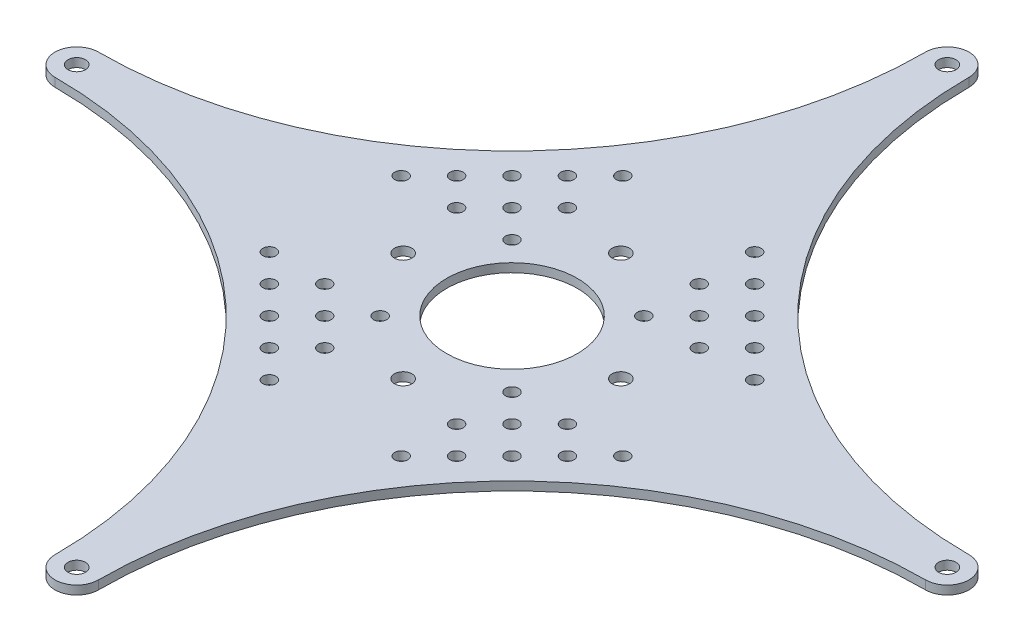
SolidWorks part; units mm, degrees
ref_plane "Front" through (0, 0, 0) normal (0, 0, 1) x (1, 0, 0)
ref_plane "Top" through (0, 0, 0) normal (0, 1, 0) x (1, 0, 0)
ref_plane "Right" through (0, 0, 0) normal (1, 0, 0) x (0, 0, -1)
sketch "Эскиз1" plane through (0, 0, 0) normal (0, 1, 0) x (1, 0, 0)
  line L0 (-100, 0) -> (0, 0) construction
  line L1 (0, 0) -> (100, 0) construction
  line L2 (100, 0) -> (0, 0) construction
  line L3 (0, 100) -> (0, 0) construction
  line L4 (0, -100) -> (0, 0) construction
  arc A0 (-5, 100) -> (5, 100) centre (0, 100) cw
  arc A1 (-100, -5) -> (-100, 5) centre (-100, 0) cw
  arc A2 (-100, 5) -> (-5, 100) centre (-100, 100) ccw
  arc A3 (-5, -100) -> (5, -100) centre (0, -100) ccw
  arc A4 (100, 5) -> (100, -5) centre (100, 0) cw
  arc A5 (-100, -5) -> (-5, -100) centre (-100, -100) cw
  arc A6 (100, -5) -> (5, -100) centre (100, -100) ccw
  arc A7 (5, 100) -> (100, 5) centre (100, 100) ccw
  dimension "D1" = 5
  dimension "D2" = 95
  dimension "D3" = 200
extrude "основа" add sketch "Эскиз1" along normal blind 2
sketch "Эскиз2" plane through (0, 2, 0) normal (0, 1, 0) x (1, 0, 0)
  line L0 (100, 0) -> (0, 0) construction
  circle A0 centre (100, 0) radius 2
  arc A4 (100, -5) -> (100, 5) centre (100, 0) ccw construction
  circle A5 centre (25, 0) radius 2
  dimension "D1" = 4
  dimension "D2" = 75
extrude "отверстия под балку" cut sketch "Эскиз2" against normal through all
sketch "ось" plane through (0, 0, 0) normal (1, 0, 0) x (0, 0, -1)
  line L0 (0, 2) -> (0, 0) construction
  line L1 (5, 2) -> (-5, 2) construction
pattern_circular "отверстия под балки" count 4 over 360 about axis through (0, 0, 0) along (0, 1, 0) of "отверстия под балку"
sketch "Эскиз4" plane through (0, 2, 0) normal (0, 1, 0) x (1, 0, 0)
  circle A0 centre (0, 0) radius 15
  dimension "D1" = 30
extrude "отверстие центр" cut sketch "Эскиз4" against normal through all
sketch "Эскиз5" plane through (0, 2, 0) normal (0, 1, 0) x (1, 0, 0)
  line L0 (0, 0) -> (32.8249, 32.8249) construction
  line L1 (40.603, 15.1472) -> (27.8751, 27.8751) construction
  circle A0 centre (40.603, 15.1472) radius 1.5
  circle A1 centre (34.2391, 8.7832) radius 1.5 [skipped]
  circle A2 centre (27.8751, 2.4193) radius 1.5 [skipped]
  circle A3 centre (27.8751, 15.1472) radius 1.5
  arc A4 (5, 100) -> (100, 5) centre (100, 100) ccw construction
  circle A6 centre (21.5111, 8.7832) radius 1.5 [skipped]
  circle A7 centre (21.5111, 21.5111) radius 1.5
  circle A8 centre (15.1472, 15.1472) radius 1.5
  circle A9 centre (15.1472, 27.8751) radius 1.5
  circle A10 centre (8.7832, 21.5111) radius 1.5 [skipped]
  circle A11 centre (8.7832, 34.2391) radius 1.5 [skipped]
  circle A12 centre (2.4193, 27.8751) radius 1.5 [skipped]
  circle A13 centre (34.2391, 21.5111) radius 1.5
  circle A14 centre (27.8751, 27.8751) radius 1.5
  circle A15 centre (21.5111, 34.2391) radius 1.5
  circle A16 centre (15.1472, 40.603) radius 1.5
  dimension "D1" = 18
  dimension "D2" = 3
  dimension "D3" = 7
  dimension "D4" = 3
  dimension "D5" = 5
extrude "отверстия под детали" cut sketch "Эскиз5" against normal through all
pattern_circular "Круговой массив2" count 4 over 360 about axis through (0, 0, 0) along (0, 1, 0) of "отверстия под детали"
equation "\"thick\"= \"текстолит@сборка.SLDASM\""
equation "\"D1@основа\"=\"thick\""
